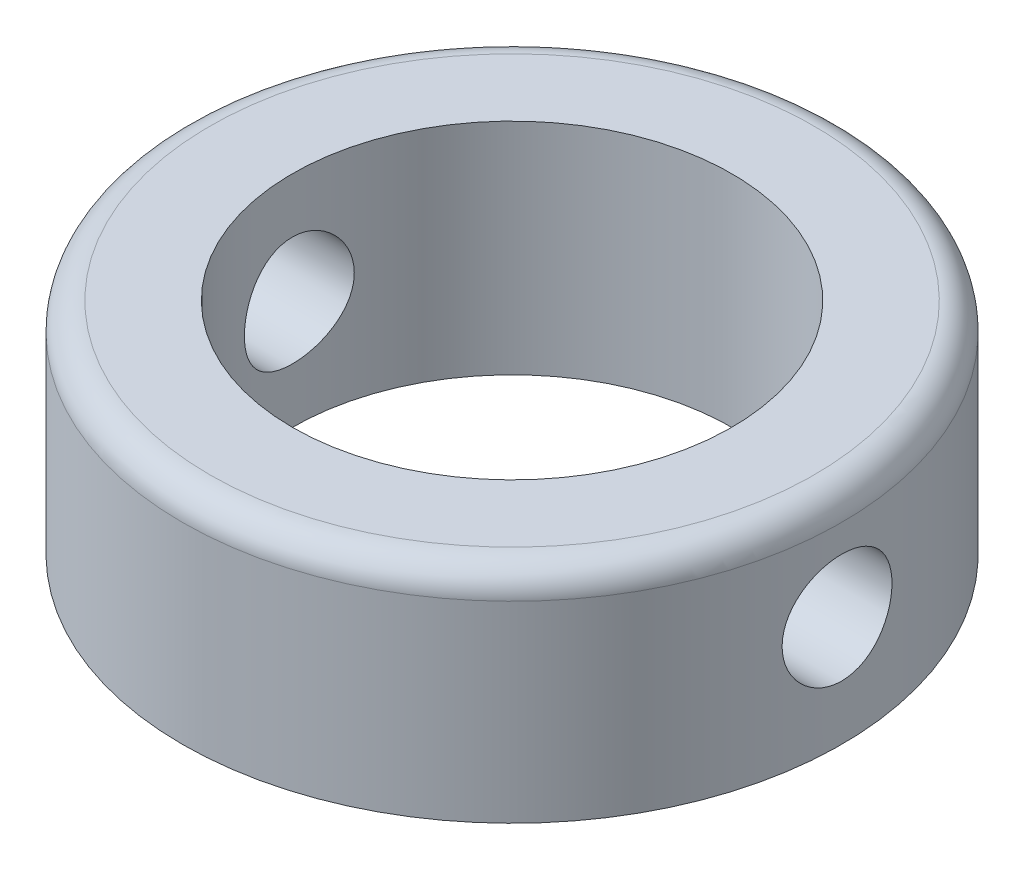
SolidWorks part; units mm, degrees
ref_plane "Front Plane" through (0, 0, 0) normal (0, 0, 1) x (1, 0, 0)
ref_plane "Top Plane" through (0, 0, 0) normal (0, 1, 0) x (1, 0, 0)
ref_plane "Right Plane" through (0, 0, 0) normal (1, 0, 0) x (0, 0, -1)
sketch "Sketch1" plane through (0, 0, 0) normal (0, 1, 0) x (1, 0, 0)
  circle A0 centre (0, 0) radius 8
  circle A1 centre (0, 0) radius 12
  dimension "D1" = 16
  dimension "D2" = 24
extrude "Boss-Extrude1" add sketch "Sketch1" along normal blind 8
fillet "Fillet1" radius 1 1 edges at (0, 8, 12)
sketch "Sketch2" plane through (0, 0, 0) normal (1, 0, 0) x (0, 0, -1)
  circle A0 centre (0, 4) radius 2
  dimension "D1" = 4
  dimension "D2" = 4
extrude "Cut-Extrude1" cut sketch "Sketch2" against normal mid plane 48
